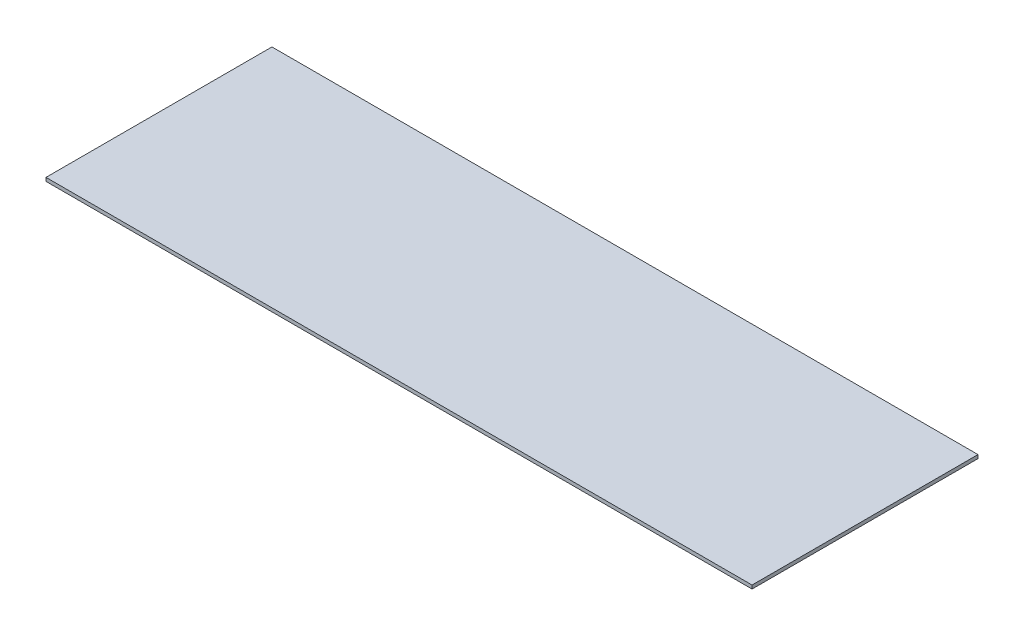
SolidWorks part; units mm, degrees
ref_plane "Front Plane" through (0, 0, 0) normal (0, 0, 1) x (1, 0, 0)
ref_plane "Top Plane" through (0, 0, 0) normal (0, 1, 0) x (1, 0, 0)
ref_plane "Right Plane" through (0, 0, 0) normal (1, 0, 0) x (0, 0, -1)
sketch "Sketch1" plane through (0, 0, 0) normal (0, 1, 0) x (1, 0, 0)
  line L1 (-317.5, -101.6) -> (317.5, -101.6)
  line L2 (-317.5, -101.6) -> (-317.5, 101.6)
  line L3 (-317.5, 101.6) -> (317.5, 101.6)
  line L4 (317.5, -101.6) -> (317.5, 101.6)
  line L5 (-317.5, -101.6) -> (317.5, 101.6) construction
  line L6 (-317.5, 101.6) -> (317.5, -101.6) construction
  point P0 (0, 0)
  dimension "D1" = 635
  dimension "D2" = 203.2
extrude "Boss-Extrude1" add sketch "Sketch1" along normal mid plane 3.175
